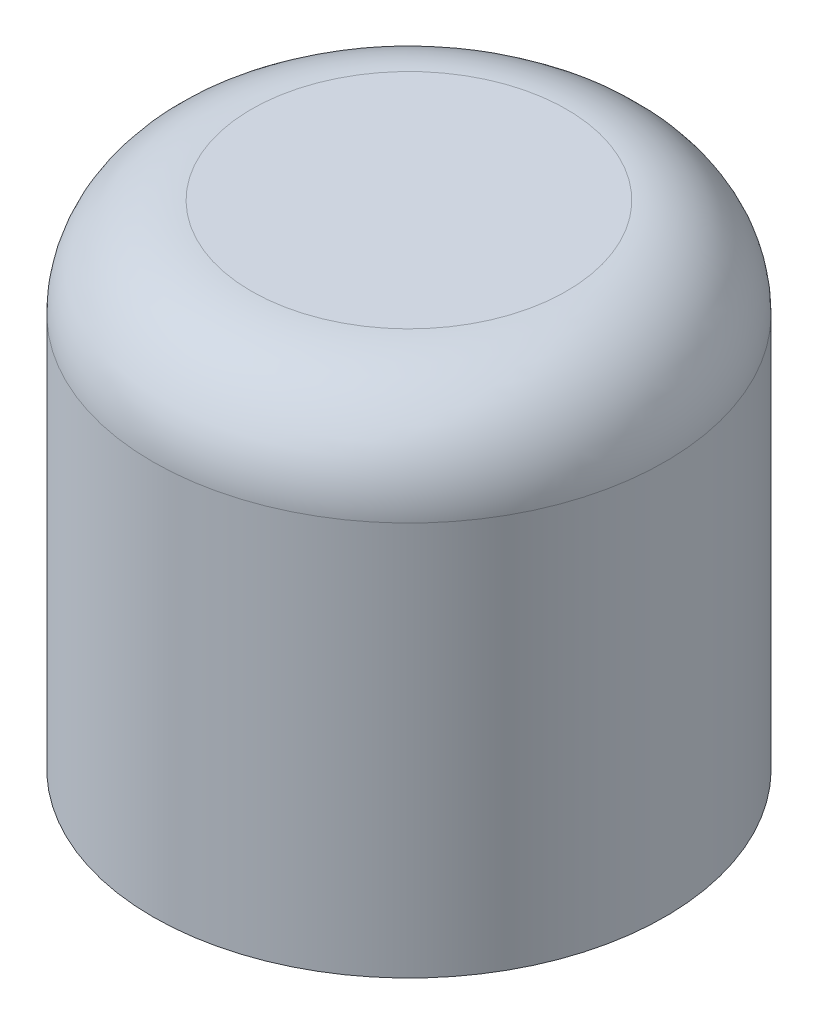
SolidWorks part; units mm, degrees
ref_plane "Front Plane" through (0, 0, 0) normal (0, 0, 1) x (1, 0, 0)
ref_plane "Top Plane" through (0, 0, 0) normal (0, 1, 0) x (1, 0, 0)
ref_plane "Right Plane" through (0, 0, 0) normal (1, 0, 0) x (0, 0, -1)
sketch "Sketch1" plane through (0, 0, 0) normal (0, 1, 0) x (1, 0, 0)
  circle A0 centre (0, 0) radius 2.6
  dimension "D1" = 5.2
extrude "Boss-Extrude1" add sketch "Sketch1" along normal blind 5
fillet "Fillet1" radius 1 1 edges at (0, 5, 2.6)
